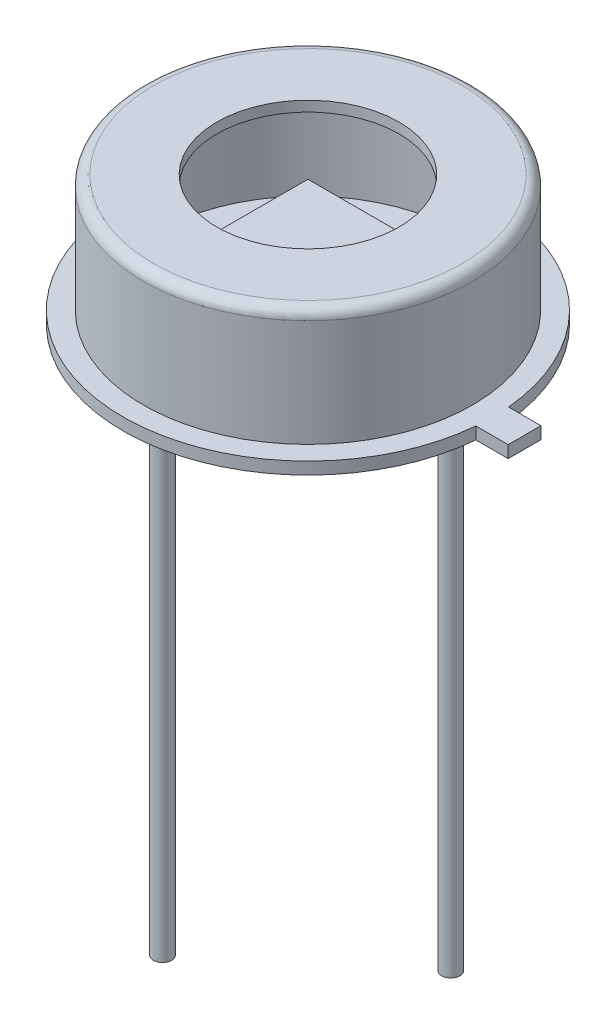
SolidWorks part; units mm, degrees
ref_plane "Front Plane" through (0, 0, 0) normal (0, 0, 1) x (1, 0, 0)
ref_plane "Top Plane" through (0, 0, 0) normal (0, 1, 0) x (1, 0, 0)
ref_plane "Right Plane" through (0, 0, 0) normal (1, 0, 0) x (0, 0, -1)
sketch "Sketch1" plane through (0, 0, 0) normal (0, 0, 1) x (1, 0, 0)
  line L0 (0, 0) -> (0, 37.7864) construction
  line L2 (4.57, 0) -> (4.57, 0.3)
  line L3 (4.57, 0.3) -> (4.065, 0.3)
  line L6 (4.065, 0.3) -> (4.065, 2.946)
  line L7 (3.811, 3.2) -> (2.25, 3.2)
  arc A0 (4.065, 2.946) -> (3.811, 3.2) centre (3.811, 2.946) ccw
  dimension "D7" = 0.254
  dimension "D1" = 0.3
  dimension "D2" = 8.13
  dimension "D4" = 9.14
  dimension "D6" = 3.2
  dimension "D8" = 4.5
revolve "Revolve-Thin2" add sketch "Sketch1" angle 360 about L0
sketch "Sketch2" plane through (0, 0, 0) normal (0, -1, 0) x (1, 0, 0)
  circle A1 centre (0, 0) radius 4.57
  circle A2 centre (0, 0) radius 4.57
  dimension "D1" = 0
extrude "Boss-Extrude1" add sketch "Sketch2" against normal up to surface (0.046 mm away) up to face at (0, 0.046, -3.811)
sketch "Sketch3" plane through (0, 0, 0) normal (0, -1, 0) x (1, 0, 0)
  line L0 (1.25, 1.25) -> (-1.25, -1.25) construction
  line L1 (-1.25, 1.25) -> (1.25, 1.25)
  line L2 (-1.25, 1.25) -> (-1.25, -1.25)
  line L3 (-1.25, -1.25) -> (1.25, -1.25)
  line L4 (1.25, 1.25) -> (1.25, -1.25)
  dimension "D1" = 2.5
extrude "Boss-Extrude2" add sketch "Sketch3" along normal blind 0.05 from offset 1.8 separate body offset against normal yes
sketch "Sketch8" plane through (0, 1.8, 0) normal (0, 1, 0) x (-1, 0, 0)
  line L1 (-1.1, 1.1) -> (1.1, 1.1)
  line L2 (-1.1, 1.1) -> (-1.1, -1.1)
  line L3 (-1.1, -1.1) -> (1.1, -1.1)
  line L4 (1.1, 1.1) -> (1.1, -1.1)
  line L5 (-1.1, 1.1) -> (1.1, -1.1) construction
  line L6 (-1.1, -1.1) -> (1.1, 1.1) construction
  point P0 (0, 0)
  dimension "D1" = 2.2
  dimension "D2" = 2.2
extrude "Boss-Extrude6" add sketch "Sketch8" along normal blind 0.2
sketch "Sketch11" plane through (0, 0, 0) normal (0, -1, 0) x (1, 0, 0)
  line L0 (0, 0) -> (6.1157, 0) construction
  line L1 (5.352, 0) -> (5.352, -0.405)
  line L2 (5.352, -0.405) -> (4.552, -0.405)
  line L3 (5.352, 0) -> (5.352, 0.405)
  line L4 (5.352, 0.405) -> (4.552, 0.405)
  line L5 (0, 0) -> (0, 6.1969) construction
  circle A0 centre (0, 0) radius 4.57
  circle A1 centre (0, 0) radius 4.57 construction
  circle M1 centre (0, 0) radius 4.57
  dimension "D4" = 9.14
  dimension "D1" = 0.405
  dimension "D2" = 0.8
  dimension "D3" = 270
  dimension "D5" = 0.405
extrude "Boss-Extrude8" add sketch "Sketch11" against normal up to surface (0.3 mm away) contours L3 L4 L2 L1 M1 up to face at (0, 0.3, -4.065)
sketch "Sketch5" plane through (0, 0, 0) normal (0, -1, 0) x (1, 0, 0)
  line L0 (0, 0) -> (-1.7961, 1.7961) construction
  line L1 (0, 0) -> (2.54, 0) construction
  line L2 (0, 0) -> (-0.8564, -1.0317) construction
  line L3 (5.352, -0.405) -> (5.352, 0.405) construction
  circle A0 centre (0, 0) radius 2.54 construction
  circle A1 centre (2.0961, -1.4346) radius 0.225
  circle A3 centre (-1.7961, 1.7961) radius 0.225
  dimension "D1" = 5.08
  dimension "D2" = 135
  dimension "D3" = 3.256
  dimension "D5" = 0.45
extrude "Boss-Extrude4" add sketch "Sketch5" along normal blind 13.5
sketch "Sketch7" [suppressed] plane through (0, 0, 0) normal (0, -1, 0) x (1, 0, 0)
  circle A0 centre (-1.7961, 1.7961) radius 0.75
  dimension "D1" = 1.5
extrude "Boss-Extrude5" [suppressed] add sketch "Sketch7" along normal blind 0.4
sketch "Sketch9" plane through (0, 0, 0) normal (0, -1, 0) x (1, 0, 0)
  circle A0 centre (0, -3.8) radius 0.5
  dimension "D1" = 1
  dimension "D2" = 3.8
extrude "Boss-Extrude7" [suppressed] add sketch "Sketch9" along normal blind 0.01
